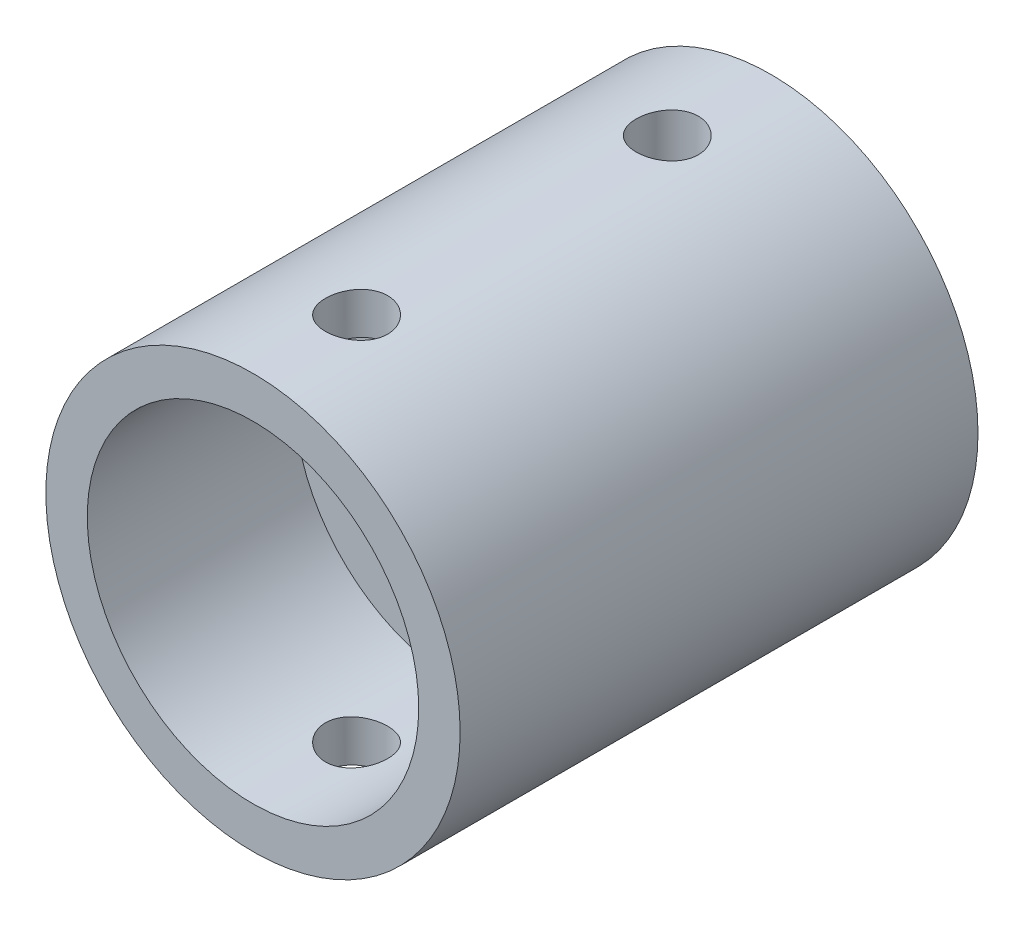
SolidWorks part; units mm, degrees
ref_plane "Plan de face" through (0, 0, 0) normal (0, 0, 1) x (1, 0, 0)
ref_plane "Plan de dessus" through (0, 0, 0) normal (0, 1, 0) x (1, 0, 0)
ref_plane "Plan de droite" through (0, 0, 0) normal (1, 0, 0) x (0, 0, -1)
sketch "Esquisse1" plane through (0, 0, 0) normal (0, 0, 1) x (1, 0, 0)
  circle A0 centre (0, 0) radius 10.25
  circle A1 centre (0, 0) radius 20
  dimension "D1" = 20.5
  dimension "D2" = 40
extrude "Boss.-Extru.1" add sketch "Esquisse1" along normal blind 50
sketch "Esquisse2" plane through (0, 0, 50) normal (0, 0, 1) x (1, 0, 0)
  circle A0 centre (0, 0) radius 16
  dimension "D1" = 32
extrude "Enlèv. mat.-Extru.1" cut sketch "Esquisse2" against normal blind 20
sketch "Esquisse3" plane through (0, 0, 0) normal (0, 1, 0) x (1, 0, 0)
  line L0 (0, 0) -> (0, -50) construction
  line L1 (-20, -50) -> (20, -50) construction
  line L2 (-16, -50) -> (16, -50) construction
  circle A0 centre (0, -10) radius 3
  circle A1 centre (0, -40) radius 3
  dimension "D1" = 6
  dimension "D2" = 10
  dimension "D3" = 10
extrude "Enlèv. mat.-Extru.2" cut sketch "Esquisse3" against normal through all and the other way through all
sketch "Esquisse4" plane through (0, 0, 50) normal (0, 0, 1) x (1, 0, 0)
  line L1 (7.9622, 13.4016) -> (-7.6251, 13.5963)
  line L2 (-7.6251, 13.5963) -> (-15.5872, 0.1946) construction
  line L3 (-15.5872, 0.1946) -> (-7.9622, -13.4016)
  line L4 (-7.9622, -13.4016) -> (7.6251, -13.5963)
  line L5 (7.6251, -13.5963) -> (15.5872, -0.1946)
  line L6 (15.5872, -0.1946) -> (7.9622, 13.4016)
  circle A0 centre (0, 0) radius 13.5 construction
  dimension "D1" = 27
